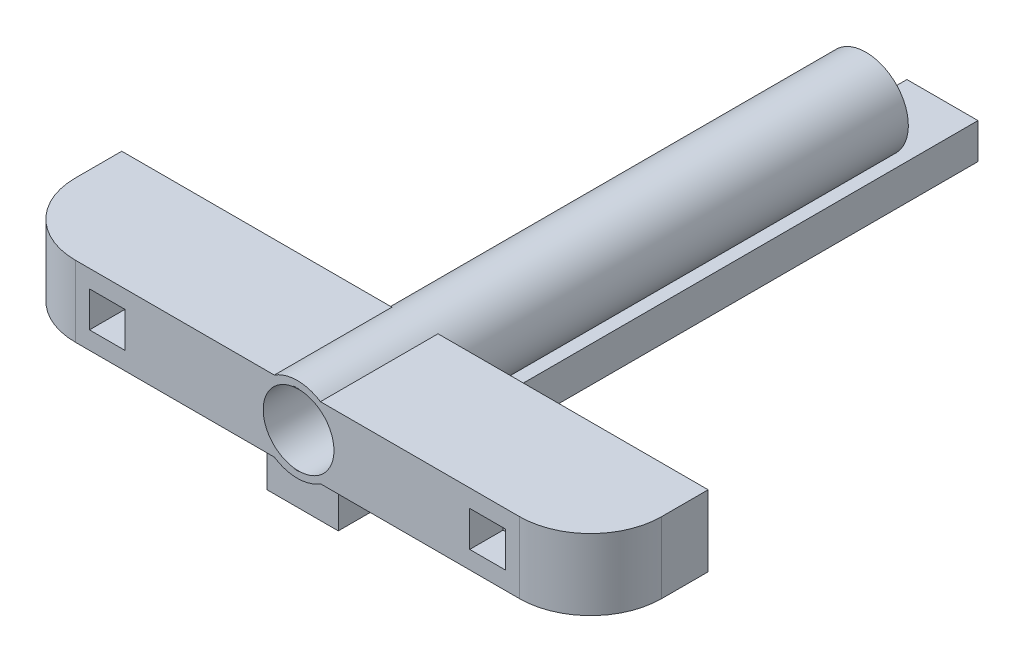
SolidWorks part; units mm, degrees
ref_plane "Plan de face" through (0, 0, 0) normal (0, 0, 1) x (1, 0, 0)
ref_plane "Plan de dessus" through (0, 0, 0) normal (0, 1, 0) x (1, 0, 0)
ref_plane "Plan de droite" through (0, 0, 0) normal (1, 0, 0) x (0, 0, -1)
sketch "Esquisse1" plane through (0, 0, 0) normal (0, 1, 0) x (1, 0, 0)
  line L1 (-56.9339, -8.2715) -> (25.5661, -8.2715)
  line L2 (-56.9339, -8.2715) -> (-56.9339, -24.8146)
  line L3 (-56.9339, -24.8146) -> (25.5661, -24.8146)
  line L4 (25.5661, -8.2715) -> (25.5661, -24.8146)
  dimension "D1" = 82.5
extrude "Boss.-Extru.1" add sketch "Esquisse1" along normal blind 10
fillet "Congé1" radius 10 2 edges at (25.5661, 5, 24.8146) (-56.9339, 5, 24.8146)
sketch "Esquisse2" plane through (0, 0, 24.8146) normal (0, 0, 1) x (1, 0, 0)
  line L0 (-46.9339, 10) -> (-46.9339, 0) construction
  line L1 (-44.9339, 7.5) -> (-39.9339, 7.5)
  line L2 (-44.9339, 7.5) -> (-44.9339, 2.5)
  line L3 (-44.9339, 2.5) -> (-39.9339, 2.5)
  line L4 (-39.9339, 7.5) -> (-39.9339, 2.5)
  line L5 (-46.9339, 10) -> (15.5661, 10) construction
  dimension "D1" = 5
  dimension "D2" = 5
  dimension "D3" = 2
  dimension "D4" = 2.5
extrude "Enlèv. mat.-Extru.2" cut sketch "Esquisse2" against normal blind 21
sketch "Esquisse4" plane through (0, 0, 24.8146) normal (0, 0, 1) x (1, 0, 0)
  line L0 (-46.9339, 10) -> (15.5661, 10) construction
  line L1 (8.5661, 7.5) -> (13.5661, 7.5)
  line L2 (8.5661, 7.5) -> (8.5661, 2.5)
  line L3 (8.5661, 2.5) -> (13.5661, 2.5)
  line L4 (13.5661, 7.5) -> (13.5661, 2.5)
  line L5 (15.5661, 0) -> (15.5661, 10) construction
  dimension "D1" = 5
  dimension "D2" = 5
  dimension "D3" = 2.5
  dimension "D4" = 2
extrude "Enlèv. mat.-Extru.3" cut sketch "Esquisse4" against normal blind 100
sketch "Esquisse5" plane through (0, 0, 24.8146) normal (0, 0, 1) x (1, 0, 0)
  line L0 (-46.9339, 10) -> (15.5661, 10) construction
  line L1 (15.5661, 0) -> (15.5661, 10) construction
  circle A0 centre (-15.6839, 5) radius 5.0298
  circle A1 centre (-15.6839, 5) radius 5.96
  dimension "D1" = 5
  dimension "D2" = 31.25
extrude "Boss.-Extru.4" add sketch "Esquisse5" against normal blind 80
sketch "Esquisse8" plane through (0, 0, 24.8146) normal (0, 0, 1) x (1, 0, 0)
  line L0 (-12.4401, 10) -> (15.5661, 10) construction
  circle A0 centre (-15.5146, 5) radius 4.9793
  dimension "D1" = 5
extrude "Enlèv. mat.-Extru.5" cut sketch "Esquisse8" against normal blind 80
sketch "Esquisse9" plane through (0, 0, 0) normal (0, 1, 0) x (1, 0, 0)
  line L1 (-35.3359, -20.1352) -> (9.2796, -20.1352)
  line L2 (-35.3359, -20.1352) -> (-35.3359, -10.1498)
  line L3 (-35.3359, -10.1498) -> (9.2796, -10.1498)
  line L4 (9.2796, -20.1352) -> (9.2796, -10.1498)
extrude "Boss.-Extru.5" add sketch "Esquisse9" along normal blind 10
sketch "Esquisse10" plane through (0, 0, 0) normal (0, -1, 0) x (-1, 0, 0)
  line L0 (-25.5661, -14.8146) -> (-25.5661, -8.2715) construction
  line L1 (20.4339, -24.3058) -> (10.4339, -24.3058)
  line L2 (20.4339, -24.3058) -> (20.4339, -14.3058)
  line L3 (20.4339, -14.3058) -> (10.4339, -14.3058)
  line L4 (10.4339, -24.3058) -> (10.4339, -14.3058)
  dimension "D1" = 10
  dimension "D2" = 10
  dimension "D3" = 36
extrude "Boss.-Extru.6" add sketch "Esquisse10" along normal blind 5
sketch "Esquisse13" plane through (0, 0, 14.3058) normal (0, 0, -1) x (-1, 0, 0)
  line L0 (10.4339, -5) -> (10.4339, 0) construction
  line L1 (10.4339, 0) -> (20.4339, 0)
  line L2 (10.4339, 0) -> (10.4339, -5)
  line L3 (10.4339, -5) -> (20.4339, -5)
  line L4 (20.4339, 0) -> (20.4339, -5)
extrude "Boss.-Extru.7" add sketch "Esquisse13" along normal blind 80
sketch "Esquisse15" plane through (0, 0, 20.1352) normal (0, 0, 1) x (1, 0, 0)
  circle A0 centre (-15.5146, 5) radius 4.9793
extrude "Enlèv. mat.-Extru.6" cut sketch "Esquisse15" against normal blind 80
